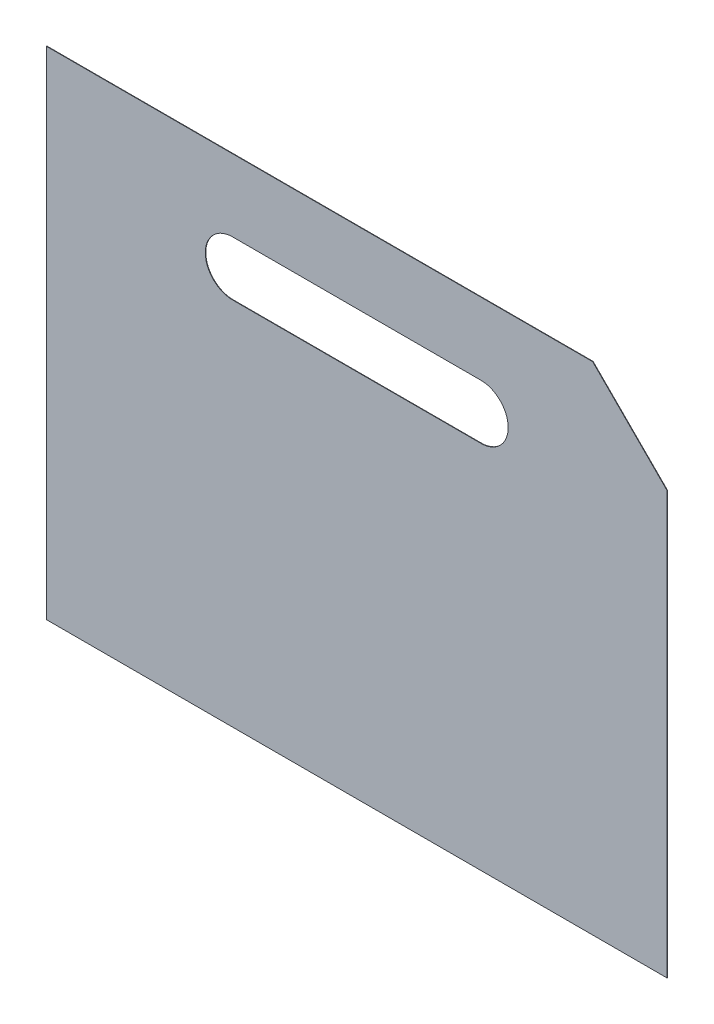
SolidWorks part; units mm, degrees
material "PET"
ref_plane "Ebene vorne" through (0, 0, 0) normal (0, 0, 1) x (1, 0, 0)
ref_plane "Ebene oben" through (0, 0, 0) normal (0, 1, 0) x (1, 0, 0)
ref_plane "Ebene rechts" through (0, 0, 0) normal (1, 0, 0) x (0, 0, -1)
sketch "Skizze1" plane through (0, 0, 0) normal (0, 0, 1) x (1, 0, 0)
  line L1 (0, 0) -> (250, 0)
  line L2 (0, 0) -> (0, 200)
  line L3 (0, 200) -> (250, 200)
  line L4 (250, 0) -> (250, 200)
  dimension "D1" = 250
  dimension "D2" = 200
extrude "Aufsatz-Linear austragen1" add sketch "Skizze1" along normal blind 0.19
sketch "Skizze2" plane through (0, 0, 0.19) normal (0, 0, 1) x (1, 0, 0)
  line L5 (75, 160) -> (175, 160) construction
  line L6 (75, 171) -> (175, 171)
  line L7 (75, 149) -> (175, 149)
  line L8 (220, 200) -> (250, 170)
  line L9 (250, 200) -> (0, 200) construction
  line L10 (250, 0) -> (250, 200) construction
  line L11 (250, 170) -> (250, 200)
  line L12 (250, 200) -> (220, 200)
  arc A0 (75, 171) -> (75, 149) centre (75, 160) ccw
  arc A1 (175, 149) -> (175, 171) centre (175, 160) ccw
  point P8 (125, 160)
  point P22 (125, 200)
  dimension "D1" = 30
  dimension "D2" = 22
  dimension "D3" = 100
  dimension "D9" = 40
extrude "Schnitt-Linear austragen1" cut sketch "Skizze2" against normal through all
